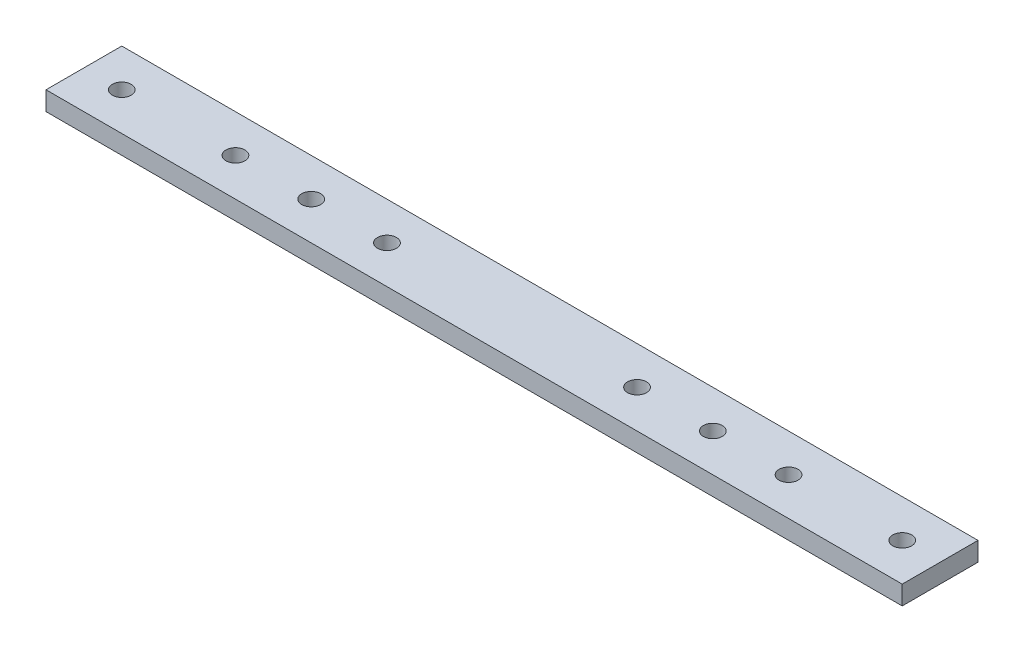
SolidWorks part; units mm, degrees
material "PBT General Purpose"
ref_plane "Front Plane" through (0, 0, 0) normal (0, 0, 1) x (1, 0, 0)
ref_plane "Top Plane" through (0, 0, 0) normal (0, 1, 0) x (1, 0, 0)
ref_plane "Right Plane" through (0, 0, 0) normal (1, 0, 0) x (0, 0, -1)
sketch "Sketch1" plane through (0, 0, 0) normal (0, 1, 0) x (1, 0, 0)
  line L1 (-143.51, 12.7) -> (143.51, 12.7)
  line L2 (-143.51, 12.7) -> (-143.51, -12.7)
  line L3 (-143.51, -12.7) -> (143.51, -12.7)
  line L4 (143.51, 12.7) -> (143.51, -12.7)
  line L5 (-143.51, 12.7) -> (143.51, -12.7) construction
  line L6 (-143.51, -12.7) -> (143.51, 12.7) construction
  point P0 (0, 0)
  dimension "D1" = 25.4
  dimension "D2" = 287.02
extrude "Boss-Extrude1" add sketch "Sketch1" along normal mid plane 6.35
sketch "Sketch2" plane through (0, 3.175, 0) normal (0, 1, 0) x (1, 0, 0)
  line L0 (0, -66.799) -> (0, 51.7077) construction
  line L1 (-143.51, 12.7) -> (-143.51, -12.7) construction
  circle A0 centre (-130.81, 0) radius 3.175
  circle A1 centre (-41.91, 0) radius 3.175
  circle A2 centre (130.81, 0) radius 3.175
  circle A3 centre (41.91, 0) radius 3.175
  circle A4 centre (-92.71, 0) radius 3.175
  circle A5 centre (-67.31, 0) radius 3.175
  circle A6 centre (67.31, 0) radius 3.175
  circle A7 centre (92.71, 0) radius 3.175
  point P18 (-143.51, 0)
  dimension "D2" = 6.35
  dimension "D1" = 12.7
  dimension "D3" = 101.6
  dimension "D4" = 25.4
  dimension "D5" = 50.8
extrude "Cut-Extrude1" cut sketch "Sketch2" against normal through all both and the other way through all
